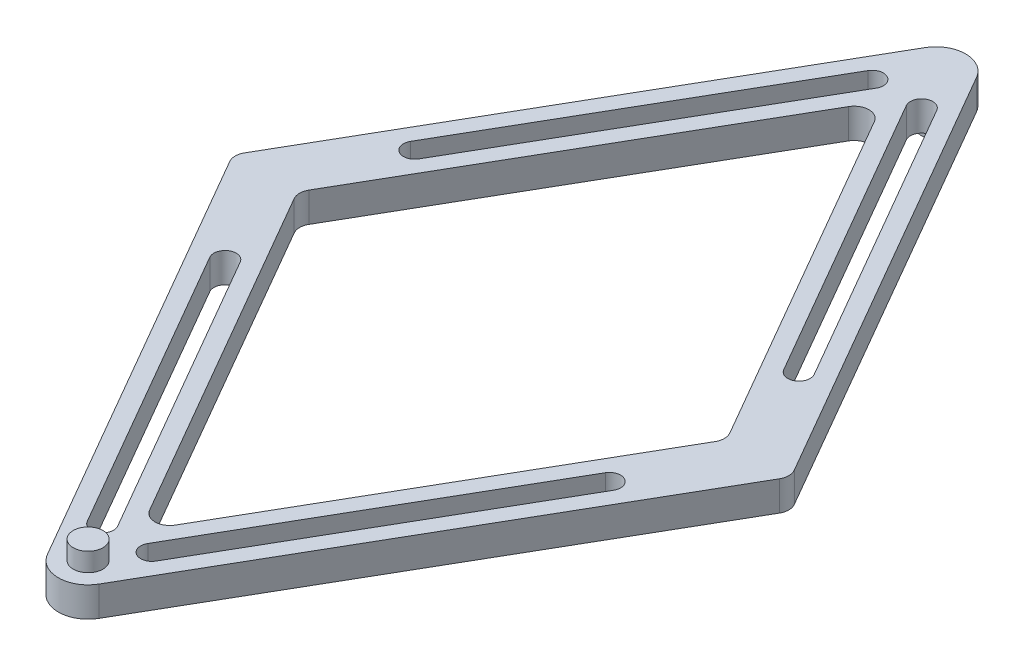
SolidWorks part; units mm, degrees
ref_plane "前视基准面" through (0, 0, 0) normal (0, 0, 1) x (1, 0, 0)
ref_plane "上视基准面" through (0, 0, 0) normal (0, 1, 0) x (1, 0, 0)
ref_plane "右视基准面" through (0, 0, 0) normal (1, 0, 0) x (0, 0, -1)
sketch "草图1" plane through (0, 0, 0) normal (0, 1, 0) x (1, 0, 0)
  line L0 (-56.2653, 0) -> (57.2053, 0) construction
  line L1 (0, -40.5882) -> (0, 41.6471) construction
  line L2 (0, -130) -> (-75.0555, 0)
  line L3 (0, -130) -> (75.0555, 0)
  line L4 (57.735, 0) -> (0, -100)
  line L5 (-57.735, 0) -> (0, -100)
  line L6 (0, 130) -> (75.0555, 0)
  line L7 (0, 130) -> (-75.0555, 0)
  line L8 (-57.735, 0) -> (0, 100)
  line L9 (57.735, 0) -> (0, 100)
  dimension "D1" = 30
  dimension "D2" = 30
  dimension "D3" = 200
extrude "凸台-拉伸1" add sketch "草图1" along normal blind 8
fillet "圆角1" radius 8 2 edges at (0, 4, 130) (0, 4, -130)
fillet "圆角2" radius 4 2 edges at (0, 4, 100) (0, 4, -100)
fillet "圆角3" radius 4 4 edges at (75.0555, 4, 0) (-75.0555, 4, 0) (-57.735, 4, 0) (57.735, 4, 0)
sketch "草图2" plane through (0, 8, 0) normal (0, 1, 0) x (1, 0, 0)
  line L0 (-66.3953, 0) -> (0, -115) construction
  line L1 (0, 0) -> (-24.2923, 0) construction
  line L2 (0, 0) -> (0, -32.5458) construction
  line L3 (-56.5803, -2) -> (-3.4641, -94) construction
  line L4 (-73.9008, -2) -> (-6.9282, -118) construction
  line L5 (-6.6454, -103.4899) -> (-51.6796, -25.4883) construction
  line L6 (-9.2435, -104.9899) -> (-54.2777, -26.9883)
  line L7 (-4.0473, -101.9899) -> (-49.0815, -23.9883)
  line L8 (6.6454, -103.4899) -> (51.6796, -25.4883) construction
  line L9 (9.2435, -104.9899) -> (54.2777, -26.9883)
  line L10 (4.0473, -101.9899) -> (49.0815, -23.9883)
  line L11 (6.6454, 103.4899) -> (51.6796, 25.4883) construction
  line L12 (9.2435, 104.9899) -> (54.2777, 26.9883)
  line L13 (4.0473, 101.9899) -> (49.0815, 23.9883)
  line L14 (-6.6454, 103.4899) -> (-51.6796, 25.4883) construction
  line L15 (-9.2435, 104.9899) -> (-54.2777, 26.9883)
  line L16 (-4.0473, 101.9899) -> (-49.0815, 23.9883)
  arc A0 (-9.2435, -104.9899) -> (-4.0473, -101.9899) centre (-6.6454, -103.4899) ccw
  arc A1 (-49.0815, -23.9883) -> (-54.2777, -26.9883) centre (-51.6796, -25.4883) ccw
  arc A2 (9.2435, -104.9899) -> (4.0473, -101.9899) centre (6.6454, -103.4899) cw
  arc A3 (49.0815, -23.9883) -> (54.2777, -26.9883) centre (51.6796, -25.4883) cw
  arc A4 (9.2435, 104.9899) -> (4.0473, 101.9899) centre (6.6454, 103.4899) ccw
  arc A5 (49.0815, 23.9883) -> (54.2777, 26.9883) centre (51.6796, 25.4883) ccw
  arc A6 (-9.2435, 104.9899) -> (-4.0473, 101.9899) centre (-6.6454, 103.4899) cw
  arc A7 (-49.0815, 23.9883) -> (-54.2777, 26.9883) centre (-51.6796, 25.4883) cw
  point P12 (-29.1625, -64.4891)
  point P19 (29.1625, -64.4891)
  point P26 (29.1625, 64.4891)
  point P33 (-29.1625, 64.4891)
  dimension "D1" = 3
extrude "切除-拉伸1" cut sketch "草图2" against normal through all
sketch "草图3" plane through (0, 8, 0) normal (0, 1, 0) x (1, 0, 0)
  circle A0 centre (0, -114) radius 4
  dimension "D1" = 8
extrude "凸台-拉伸2" add sketch "草图3" along normal blind 5 contours A0
sketch "草图4" plane through (0, 0, 0) normal (0, -1, 0) x (1, 0, 0)
  circle A1 centre (0, -114) radius 4
  dimension "D1" = 8
extrude "凸台-拉伸3" add sketch "草图4" along normal blind 5 contours A1
